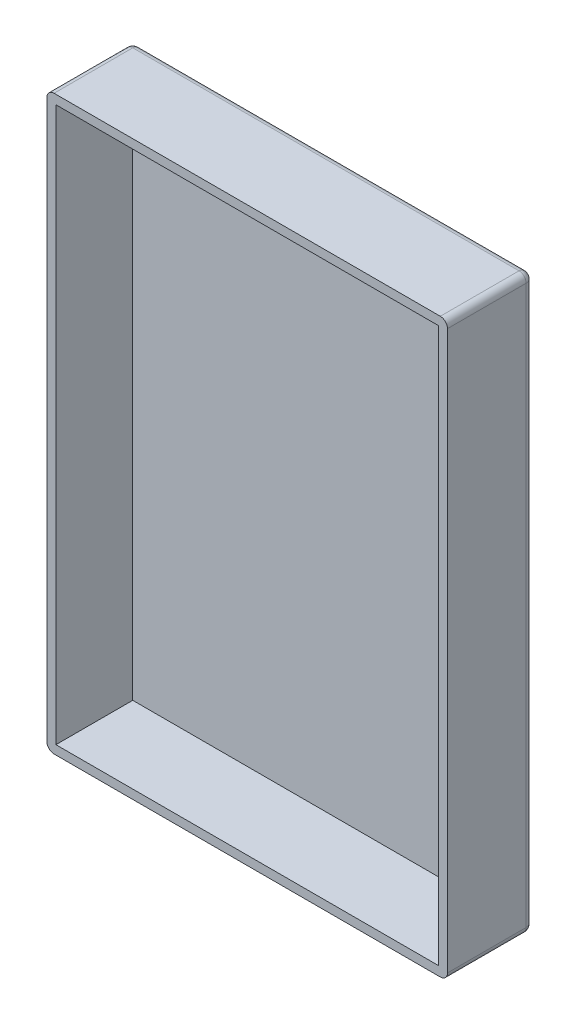
SolidWorks part; units mm, degrees
material "Thornel Mat VMA"
ref_plane "Front" through (0, 0, 0) normal (0, 0, 1) x (1, 0, 0)
ref_plane "Top" through (0, 0, 0) normal (0, 1, 0) x (1, 0, 0)
ref_plane "Right" through (0, 0, 0) normal (1, 0, 0) x (0, 0, -1)
sketch "Sketch1" plane through (0, 0, 0) normal (0, 0, 1) x (1, 0, 0)
  line L1 (-44.45, 63.5) -> (44.45, 63.5)
  line L2 (-44.45, 63.5) -> (-44.45, -63.5)
  line L3 (-44.45, -63.5) -> (44.45, -63.5)
  line L4 (44.45, 63.5) -> (44.45, -63.5)
  line L5 (-44.45, 63.5) -> (44.45, -63.5) construction
  line L6 (-44.45, -63.5) -> (44.45, 63.5) construction
  point P0 (0, 0)
  dimension "D1" = 88.9
  dimension "D2" = 127
extrude "Boss-Extrude1" add sketch "Sketch1" along normal blind 19.05
fillet "Fillet1" radius 1.5875 8 edges at (44.45, -63.5, 9.525) (44.45, 63.5, 9.525) (-44.45, -63.5, 9.525) (-44.45, 63.5, 9.525) (44.45, 0, 0) (0, -63.5, 0) (-44.45, 0, 0) (0, 63.5, 0)
shell "Shell1" thickness 2
